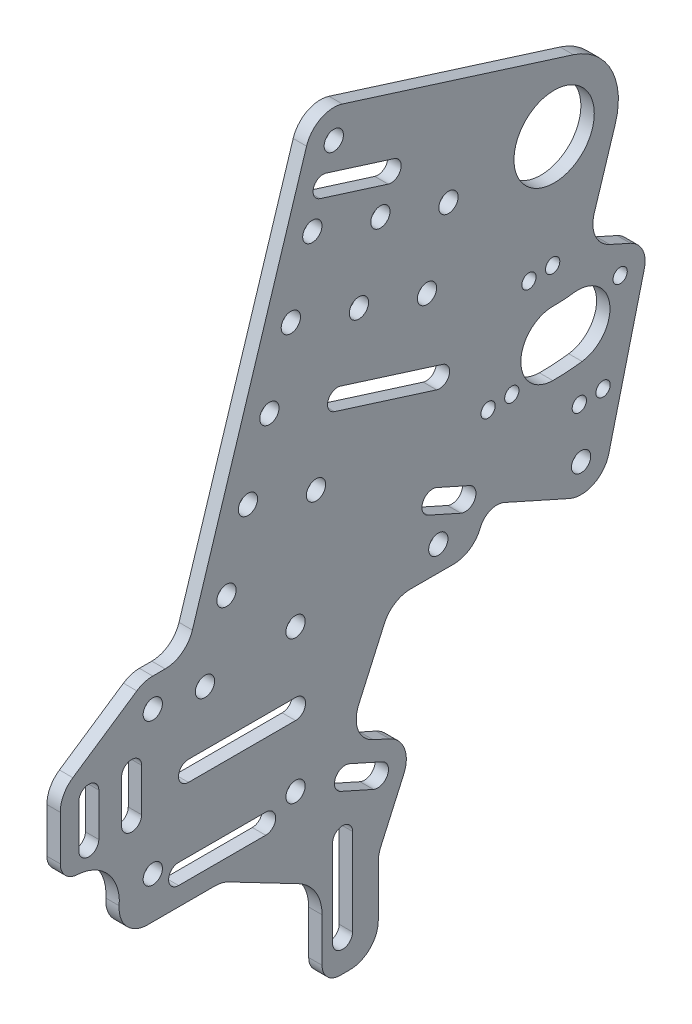
SolidWorks part; units mm, degrees
material "5052-H32"
ref_plane "Front Plane" through (0, 0, 0) normal (0, 0, 1) x (1, 0, 0)
ref_plane "Top Plane" through (0, 0, 0) normal (0, 1, 0) x (1, 0, 0)
ref_plane "Right Plane" through (0, 0, 0) normal (1, 0, 0) x (0, 0, -1)
sketch "Sketch2" plane through (0, 0, 0) normal (1, 0, 0) x (0, 0, -1)
  line L3 (55, 0) -> (-55, 0) construction
  line L9 (71.6952, 111.2048) -> (68.2175, 112.7608) construction
  line L28 (0, 0) -> (-57.2178, 40.0643) construction
  line L40 (0, 0) -> (113.3671, 198.5091) construction
  line L41 (113.3671, 198.5091) -> (58.7631, 215.7257) construction
  line L42 (99.338, 182.3162) -> (24.13, 14.224) construction
  line L44 (30.078, 221.0415) -> (54.3024, 213.4035)
  line L45 (32.2166, 227.8243) -> (56.441, 220.1864)
  line L49 (104.399, 158.5001) -> (136.8581, 143.9772) construction
  line L50 (136.8581, 143.9772) -> (122.3352, 111.518) construction
  line L51 (112.8406, 159.0638) -> (145.2997, 144.5408) construction
  line L56 (43.9148, 180.4584) -> (36.2769, 156.2339) construction
  line L57 (-29.4365, 93.5262) -> (-29.4365, 42.7262) construction
  line L61 (122.3352, 111.518) -> (89.876, 126.041) construction
  line L62 (89.876, 126.041) -> (104.399, 158.5001) construction
  line L63 (104.399, 158.5001) -> (122.3352, 111.518) construction
  line L65 (145.2997, 144.5408) -> (130.7768, 112.0817) construction
  line L66 (130.7768, 112.0817) -> (98.3176, 126.6046) construction
  line L67 (98.3176, 126.6046) -> (112.8406, 159.0638) construction
  line L68 (112.8406, 159.0638) -> (130.7768, 112.0817) construction
  line L69 (58.7631, 215.7257) -> (31.1473, 224.4329) construction
  line L70 (40.5747, 41.6494) -> (37.0969, 43.2054) construction
  line L71 (38.1, 20.2565) -> (38.1, -10.7315) construction
  line L72 (41.656, 20.2565) -> (41.656, -10.7315)
  line L73 (34.544, 20.2565) -> (34.544, -10.7315)
  line L74 (0, -14.2875) -> (38.1, -14.2875) construction
  line L75 (-20.2565, 38.1) -> (10.7315, 38.1) construction
  line L76 (-20.2565, 41.656) -> (10.7315, 41.656)
  line L77 (-20.2565, 34.544) -> (10.7315, 34.544)
  line L78 (14.2875, 38.1) -> (14.2875, 0) construction
  line L79 (-52.2013, 78.1643) -> (-52.2013, 62.9243) construction
  line L80 (-48.6453, 78.1643) -> (-48.6453, 62.9243)
  line L81 (-55.7573, 78.1643) -> (-55.7573, 62.9243)
  line L82 (-36.9613, 78.1643) -> (-36.9613, 62.9243) construction
  line L83 (-33.4053, 78.1643) -> (-33.4053, 62.9243)
  line L84 (-40.5173, 78.1643) -> (-40.5173, 62.9243)
  line L85 (31.1473, 224.4329) -> (-10.8613, 91.1986) construction
  line L86 (31.1473, 224.4329) -> (34.9663, 236.5451) construction
  line L92 (27.3284, 212.3207) -> (75.7772, 197.0448) construction
  line L93 (19.6904, 188.0963) -> (68.1392, 172.8204) construction
  line L94 (36.2769, 156.2339) -> (12.0525, 163.8719) construction
  line L95 (36.2769, 156.2339) -> (72.6135, 144.777) construction
  line L96 (37.3462, 159.6254) -> (73.6828, 148.1685)
  line L97 (35.2076, 152.8425) -> (71.5442, 141.3856)
  line L98 (36.2769, 156.2339) -> (28.639, 132.0095) construction
  line L99 (28.639, 132.0095) -> (4.4146, 139.6475) construction
  line L100 (-29.4365, 68.1262) -> (-16.7365, 68.1262) construction
  line L101 (-16.7365, 68.1262) -> (21.3635, 68.1262) construction
  line L102 (-16.7365, 71.6822) -> (21.3635, 71.6822)
  line L103 (-16.7365, 64.5702) -> (21.3635, 64.5702)
  line L104 (38.0214, 246.2349) -> (120.2412, 220.3111)
  line L105 (25.2765, 239.6003) -> (-15.3369, 110.7911)
  line L106 (-29.4365, 103.6862) -> (-25.0266, 103.6862)
  line L107 (-35.1197, 101.9481) -> (-57.8844, 86.5862)
  line L108 (-62.3613, 62.2565) -> (-62.3613, 78.1643)
  line L109 (-31.257, 27.94) -> (-7.2528, 27.94)
  line L110 (30.7975, -15.5575) -> (30.7975, 0)
  line L113 (135.1691, 191.635) -> (127.6222, 167.6992)
  line L114 (133.1625, 155.37) -> (140.4889, 152.092)
  line L115 (145.4838, 141.8254) -> (132.8214, 91.067)
  line L116 (118.8141, 84.2522) -> (95.6442, 94.6189)
  line L117 (50.8, 6.3603) -> (50.8, -11.7475)
  line L118 (37.1475, -21.9075) -> (40.64, -21.9075)
  line L120 (54.7606, 42.2589) -> (48.9643, 44.8523)
  line L121 (52.9447, 78.6256) -> (43.8397, 58.2757)
  line L122 (59.8853, 28.8354) -> (51.6859, 10.5098)
  line L123 (62.2187, 84.6362) -> (77.6364, 84.6362)
  line L124 (87.2546, 91.416) -> (86.9104, 90.6468)
  line L125 (30.7975, 0) -> (15.3035, 0) construction
  line L126 (22.4684, 13.7378) -> (-2.5545, 26.7884)
  line L127 (0, 0) -> (0, 15.494) construction
  line L128 (39.0186, 38.1716) -> (50.6112, 32.9849) construction
  line L129 (70.1392, 107.727) -> (81.7318, 102.5402) construction
  line L131 (71.6952, 111.2048) -> (83.2878, 106.018)
  line L132 (68.5832, 104.2492) -> (80.1757, 99.0625)
  line L133 (40.5747, 41.6494) -> (52.1672, 36.4626)
  line L134 (37.4626, 34.6938) -> (49.0552, 29.5071)
  circle A36 centre (0, 0) radius 14.2875 construction
  circle A37 centre (-57.2178, 40.0643) radius 14.2875 construction
  circle A38 centre (113.3671, 198.5091) radius 14.2875
  arc A39 (54.3024, 213.4035) -> (56.441, 220.1864) centre (55.3717, 216.795) ccw
  arc A40 (32.2166, 227.8243) -> (30.078, 221.0415) centre (31.1473, 224.4329) ccw
  circle A49 centre (-29.4365, 42.7262) radius 3.429
  circle A50 centre (21.3635, 93.5262) radius 3.429
  circle A51 centre (122.9635, 93.5262) radius 3.429
  circle A54 centre (104.399, 158.5001) radius 2.54
  circle A55 centre (136.8581, 143.9772) radius 2.54
  circle A56 centre (122.3352, 111.518) radius 2.54
  circle A57 centre (89.876, 126.041) radius 2.54
  arc A60 (113.3671, 135.0091) -> (121.8087, 135.5727) centre (113.3671, 198.5091) ccw construction
  circle A61 centre (112.8406, 159.0638) radius 2.54
  circle A62 centre (130.7768, 112.0817) radius 2.54
  circle A63 centre (98.3176, 126.6046) radius 2.54
  circle A64 centre (-29.4365, 93.5262) radius 3.429
  circle A65 centre (21.3635, 42.7262) radius 3.429
  circle A66 centre (72.1635, 93.5262) radius 3.429
  arc A67 (41.656, 20.2565) -> (34.544, 20.2565) centre (38.1, 20.2565) ccw
  arc A68 (34.544, -10.7315) -> (41.656, -10.7315) centre (38.1, -10.7315) ccw
  arc A69 (-20.2565, 41.656) -> (-20.2565, 34.544) centre (-20.2565, 38.1) ccw
  arc A70 (10.7315, 34.544) -> (10.7315, 41.656) centre (10.7315, 38.1) ccw
  arc A71 (-48.6453, 78.1643) -> (-55.7573, 78.1643) centre (-52.2013, 78.1643) ccw
  arc A72 (-55.7573, 62.9243) -> (-48.6453, 62.9243) centre (-52.2013, 62.9243) ccw
  arc A73 (-33.4053, 78.1643) -> (-40.5173, 78.1643) centre (-36.9613, 78.1643) ccw
  arc A74 (-40.5173, 62.9243) -> (-33.4053, 62.9243) centre (-36.9613, 62.9243) ccw
  circle A75 centre (34.9663, 236.5451) radius 3.429
  circle A76 centre (27.3284, 212.3207) radius 3.429
  circle A77 centre (19.6904, 188.0963) radius 3.429
  circle A78 centre (12.0525, 163.8719) radius 3.429
  circle A79 centre (4.4146, 139.6475) radius 3.429
  circle A80 centre (-3.2234, 115.423) radius 3.429
  circle A81 centre (-10.8613, 91.1986) radius 3.429
  circle A82 centre (51.5528, 204.6828) radius 3.429
  circle A83 centre (43.9148, 180.4584) radius 3.429
  circle A84 centre (75.7772, 197.0448) radius 3.429
  circle A85 centre (68.1392, 172.8204) radius 3.429
  arc A86 (37.3462, 159.6254) -> (35.2076, 152.8425) centre (36.2769, 156.2339) ccw
  arc A87 (71.5442, 141.3856) -> (73.6828, 148.1685) centre (72.6135, 144.777) ccw
  circle A88 centre (28.639, 132.0095) radius 3.429
  arc A89 (-16.7365, 71.6822) -> (-16.7365, 64.5702) centre (-16.7365, 68.1262) ccw
  arc A90 (21.3635, 64.5702) -> (21.3635, 71.6822) centre (21.3635, 68.1262) ccw
  arc A91 (38.0214, 246.2349) -> (25.2765, 239.6003) centre (34.9663, 236.5451) ccw
  arc A92 (120.2412, 220.3111) -> (135.1691, 191.635) centre (113.3671, 198.5091) cw
  arc A93 (-35.1197, 101.9481) -> (-29.4365, 103.6862) centre (-29.4365, 93.5262) cw
  arc A94 (-62.3613, 78.1643) -> (-57.8844, 86.5862) centre (-52.2013, 78.1643) cw
  arc A95 (-25.0266, 103.6862) -> (-15.3369, 110.7911) centre (-25.0266, 113.8462) ccw
  arc A96 (-56.356, 55.9159) -> (-62.3613, 62.2565) centre (-56.0113, 62.2565) cw
  arc A97 (-41.388, 38.8666) -> (-56.356, 55.9159) centre (-57.2178, 40.0643) ccw
  arc A99 (-31.257, 27.94) -> (-41.388, 38.8666) centre (-31.257, 38.1) cw
  arc A100 (37.1475, -21.9075) -> (30.7975, -15.5575) centre (37.1475, -15.5575) cw
  arc A101 (140.4889, 152.092) -> (145.4838, 141.8254) centre (136.8581, 143.9772) cw
  arc A102 (132.8214, 91.067) -> (118.8141, 84.2522) centre (122.9635, 93.5262) cw
  arc A105 (133.1625, 155.37) -> (127.6222, 167.6992) centre (137.3119, 164.644) cw
  arc A106 (121.8087, 135.5727) -> (112.9541, 135.0104) centre (113.3671, 198.5091) cw construction
  arc A107 (112.8797, 123.5807) -> (123.3282, 124.2442) centre (113.3671, 198.5091) ccw
  arc A108 (113.0284, 146.4402) -> (120.2892, 146.9013) centre (113.3671, 198.5091) ccw
  arc A109 (113.0284, 146.4402) -> (112.8797, 123.5807) centre (112.9541, 135.0104) ccw
  arc A110 (123.3282, 124.2442) -> (120.2892, 146.9013) centre (121.8087, 135.5727) ccw
  arc A111 (40.64, -21.9075) -> (50.8, -11.7475) centre (40.64, -11.7475) ccw
  arc A112 (50.8, 6.3603) -> (51.6859, 10.5098) centre (60.96, 6.3603) cw
  arc A113 (54.7606, 42.2589) -> (59.8853, 28.8354) centre (50.6112, 32.9849) cw
  arc A114 (48.9643, 44.8523) -> (43.8397, 58.2757) centre (53.1137, 54.1263) cw
  arc A115 (62.2187, 84.6362) -> (52.9447, 78.6256) centre (62.2187, 74.4762) ccw
  arc A117 (77.6364, 84.6362) -> (86.9104, 90.6468) centre (77.6364, 94.7962) ccw
  arc A118 (87.2546, 91.416) -> (95.6442, 94.6189) centre (93.0509, 88.8226) cw
  arc A121 (30.7975, 0) -> (22.4684, 13.7378) centre (15.3035, 0) ccw
  arc A122 (-7.2528, 27.94) -> (-2.5545, 26.7884) centre (-7.2528, 17.78) cw
  arc A126 (71.6952, 111.2048) -> (68.5832, 104.2492) centre (70.1392, 107.727) ccw
  arc A127 (80.1757, 99.0625) -> (83.2878, 106.018) centre (81.7318, 102.5402) ccw
  arc A128 (40.5747, 41.6494) -> (37.4626, 34.6938) centre (39.0186, 38.1716) ccw
  arc A129 (49.0552, 29.5071) -> (52.1672, 36.4626) centre (50.6112, 32.9849) ccw
  point P26 (66.6614, 109.283)
  point P31 (113.3671, 135.0091)
  point P37 (2.3135, 68.1262)
  point P38 (35.5409, 39.7276)
  point P40 (75.9355, 105.1336)
  point P43 (44.8149, 35.5782)
  point P70 (54.4452, 150.5055)
  point P80 (121.8087, 135.5727)
  point P89 (38.1, 4.7625)
  point P98 (-4.7625, 38.1)
  point P100 (38.1, 23.8125)
  point P109 (-23.8125, 38.1)
  point P111 (-52.2013, 70.5443)
  point P116 (-36.9613, 70.5443)
  point P176 (117.3912, 135.1367)
  point P179 (-4.7625, 27.94)
  point P201 (64.0347, 38.1095)
  point P204 (39.6903, 49.0017)
  dimension "D1" = 28.575
  dimension "D2" = 69.85
  dimension "D5" = 25.4
  dimension "D6" = 3.556
  dimension "D7" = 184.15
  dimension "D8" = 28.0103
  dimension "D9" = 7.62
  dimension "D10" = 10.16
  dimension "D11" = 27.7812
  dimension "D13" = 6.858
  dimension "D15" = 53.4619
  dimension "D17" = 180.1812
  dimension "D18" = 53.4619
  dimension "D19" = 3.556
  dimension "D20" = 38.1
  dimension "D21" = 38.1
  dimension "D24" = 5.08
  dimension "D28" = 10.16
  dimension "D30" = 35.56
  dimension "D31" = 8.4416
  dimension "D33" = 65.895
  dimension "D34" = 35
  dimension "D35" = 60.27
  dimension "D40" = 76.2
  dimension "D16" = 7.62
  dimension "D27" = 10.16
  dimension "D47" = 38.1
  dimension "D48" = 7.112
  dimension "D50" = 38.1
  dimension "D53" = 3.556
  dimension "D56" = 12.7
  dimension "D57" = 12.7
  dimension "D58" = 25.4
  dimension "D60" = 25.4
  dimension "D61" = 25.4
  dimension "D25" = 3.556
  dimension "D63" = 6.35
  dimension "D64" = 31.75
  dimension "D65" = 10.16
  dimension "D69" = 16.51
  dimension "D70" = 12.7
  dimension "D73" = 6.35
  dimension "D74" = 8.89
  dimension "D72" = 8.89
  dimension "D75" = 11.43
  dimension "D77" = 7.2813
  dimension "D78" = 15.494
  dimension "D81" = 15.494
  dimension "D82" = 10.16
  dimension "D83" = 6.35
  dimension "D38" = 17.7847
  dimension "D3" = 228.6
  dimension "D12" = 2.6619
  dimension "D14" = 78.5812
  dimension "D22" = 35.56
  dimension "D23" = 63.5
  dimension "D26" = 12.7
  dimension "D29" = 8.4667
  dimension "D32" = 50.8
  dimension "D36" = 16.1929
  dimension "D37" = 12.7
  dimension "D39" = 76.2
  dimension "D41" = 12.7
  dimension "D43" = 17.5
  dimension "D44" = 7.112
  dimension "D45" = 3.556
  dimension "D46" = 38.1
  dimension "D49" = 38.1
  dimension "D51" = 15.24
  dimension "D52" = 15.24
  dimension "D54" = 38.1
  dimension "D55" = 23.8125
  dimension "D59" = 25.4
  dimension "D62" = 25.4
  dimension "D66" = 15.494
  dimension "D67" = 3
  dimension "D68" = 25.4
  dimension "D71" = 7.62
  dimension "D76" = 60.8098
extrude "Boss-Extrude1" add sketch "Sketch2" along normal blind 4.7625
sketch "Sketch3" plane through (4.7625, 0, 0) normal (1, 0, 0) x (0, 0, -1)
  text T0 "3597" font "A4 SPEED" height 11.43
  dimension "D1" = 106.68
  dimension "D2" = 5.08
extrude "Cut-Extrude1" [suppressed] cut sketch "Sketch3" against normal through all
